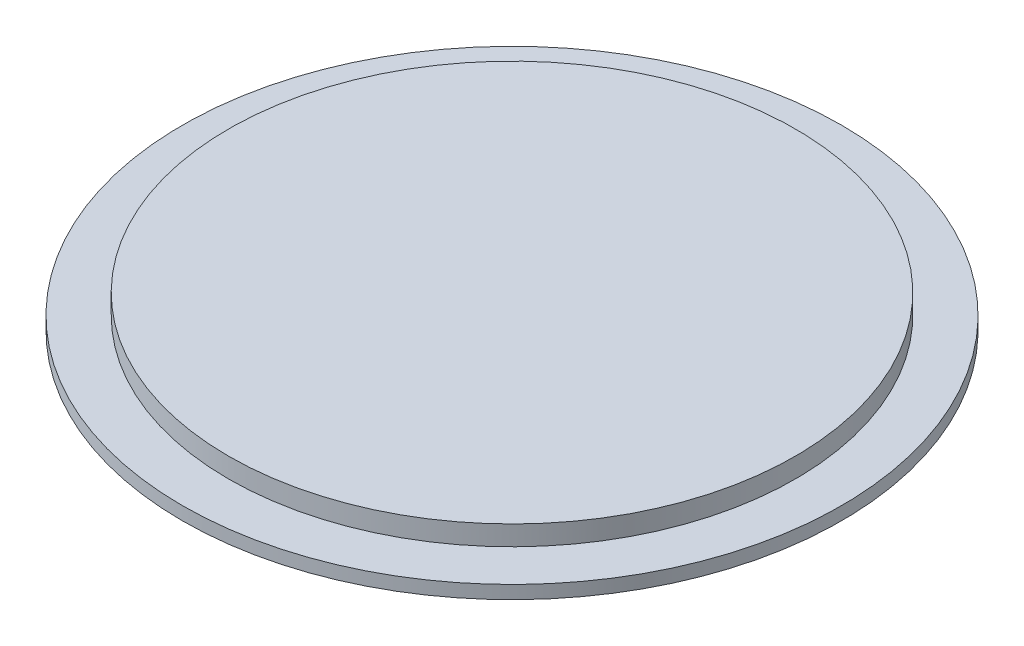
SolidWorks part; units mm, degrees
ref_plane "Front Plane" through (0, 0, 0) normal (0, 0, 1) x (1, 0, 0)
ref_plane "Top Plane" through (0, 0, 0) normal (0, 1, 0) x (1, 0, 0)
ref_plane "Right Plane" through (0, 0, 0) normal (1, 0, 0) x (0, 0, -1)
sketch "Sketch1" plane through (0, 0, 0) normal (0, 1, 0) x (1, 0, 0)
  circle A0 centre (0, 0) radius 25
  dimension "D1" = 50
extrude "Boss-Extrude1" add sketch "Sketch1" along normal blind 1
sketch "Sketch2" plane through (0, 1, 0) normal (0, 1, 0) x (1, 0, 0)
  circle A0 centre (0, 0) radius 21.5
  dimension "D1" = 43
extrude "Boss-Extrude2" add sketch "Sketch2" along normal blind 1.5
